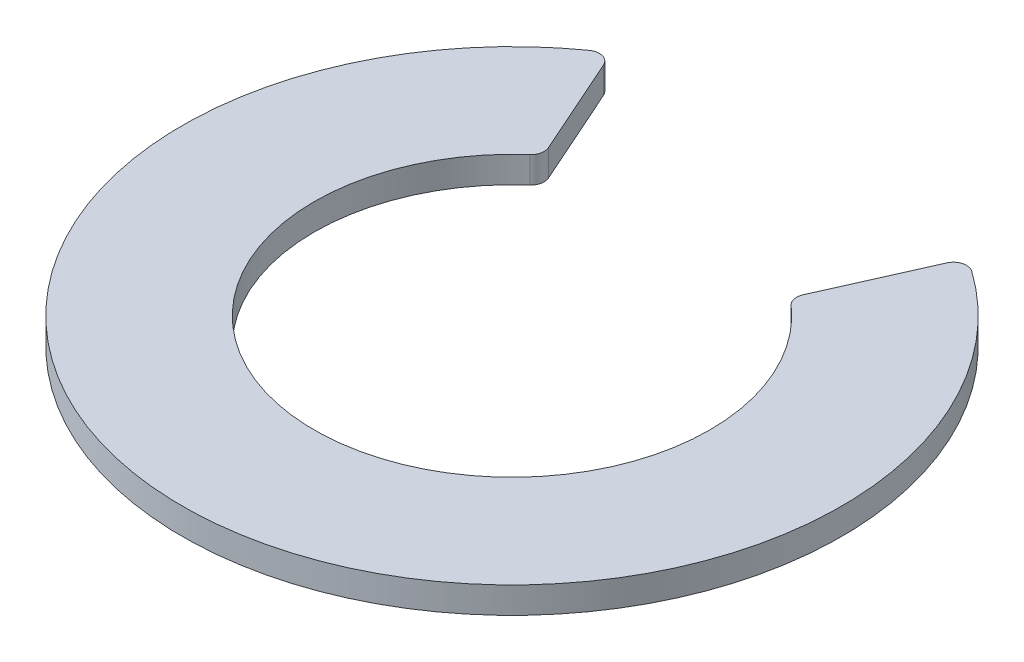
SolidWorks part; units mm, degrees
ref_plane "Front Plane" through (0, 0, 0) normal (0, 0, 1) x (1, 0, 0)
ref_plane "Top Plane" through (0, 0, 0) normal (0, 1, 0) x (1, 0, 0)
ref_plane "Right Plane" through (0, 0, 0) normal (1, 0, 0) x (0, 0, -1)
sketch "Sketch1" plane through (0, 0, 0) normal (0, 1, 0) x (1, 0, 0)
  line L0 (-13.0097, 19.9545) -> (-9.6583, 12.4158)
  line L1 (9.6583, 12.4158) -> (13.0097, 19.9545)
  arc A0 (-9.9113, 11.259) -> (9.9113, 11.259) centre (0, 0) ccw
  arc A1 (-14.5037, 20.3628) -> (14.5037, 20.3628) centre (0, 0) ccw
  arc A2 (14.5037, 20.3628) -> (13.0097, 19.9545) centre (13.9235, 19.5483) ccw
  arc A3 (9.9113, 11.259) -> (9.6583, 12.4158) centre (10.5721, 12.0096) cw
  arc A4 (-9.9113, 11.259) -> (-9.6583, 12.4158) centre (-10.5721, 12.0096) ccw
  arc A5 (-14.5037, 20.3628) -> (-13.0097, 19.9545) centre (-13.9235, 19.5483) cw
  point P8 (13.4946, 21.0451)
  point P11 (9.3523, 11.7275)
  point P14 (-9.3523, 11.7275)
  point P17 (-13.4946, 21.0451)
  dimension "D1" = 25
  dimension "D2" = 15
  dimension "D3" = 1
extrude "Boss-Extrude1" add sketch "Sketch1" along normal blind 2
